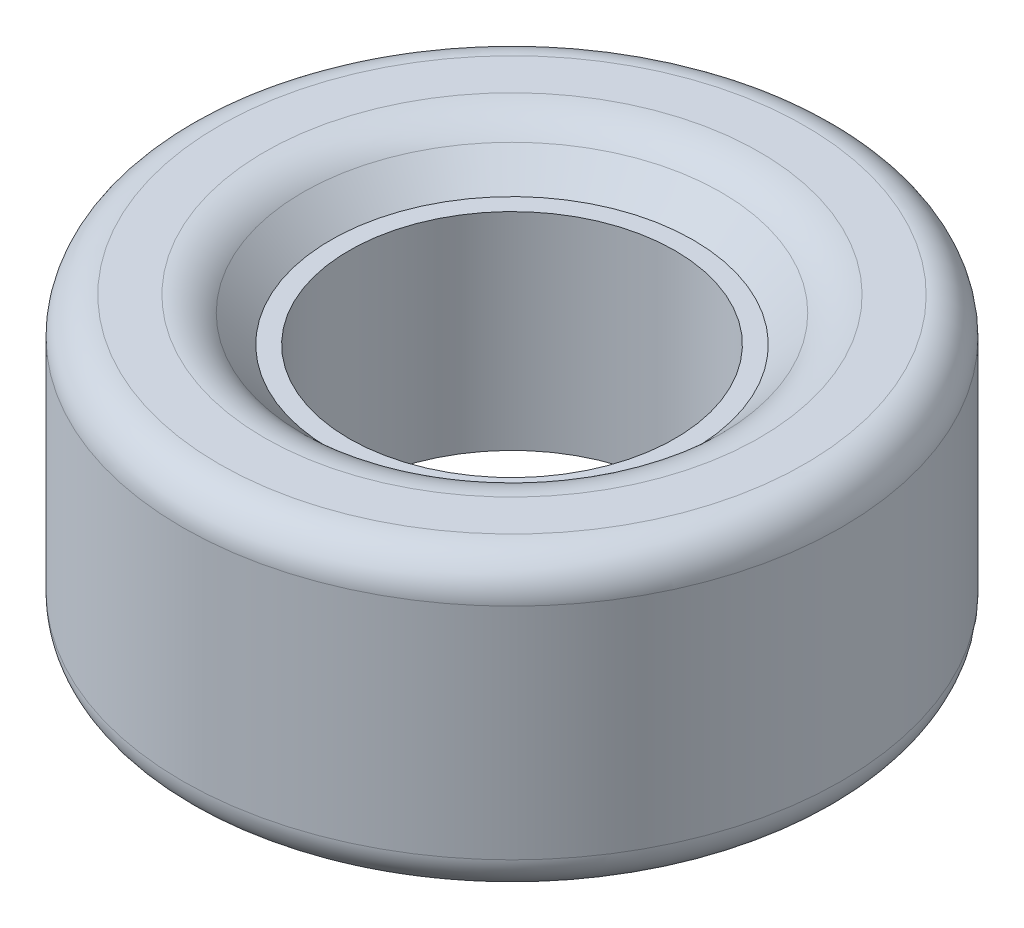
SolidWorks part; units mm, degrees
material "Rubber"
ref_plane "Front Plane" through (0, 0, 0) normal (0, 0, 1) x (1, 0, 0)
ref_plane "Top Plane" through (0, 0, 0) normal (0, 1, 0) x (1, 0, 0)
ref_plane "Right Plane" through (0, 0, 0) normal (1, 0, 0) x (0, 0, -1)
sketch "Sketch1" plane through (0, 0, 0) normal (0, 1, 0) x (1, 0, 0)
  circle A0 centre (0, 0) radius 44.5
  circle A1 centre (0, 0) radius 90
  dimension "D1" = 89
  dimension "D2" = 180
extrude "Boss-Extrude1" add sketch "Sketch1" along normal blind 80
ref_plane "Plane1" through (0, 40, 0) normal (0, -1, 0) x (-1, 0, 0)
sketch "Sketch2" plane through (0, 0, 0) normal (0, 0, 1) x (1, 0, 0)
  line L0 (0, 0) -> (0, 80) construction
  line L1 (-44.5, 0) -> (44.5, 0) construction
  line L2 (44.5, 80) -> (-44.5, 80) construction
  line L3 (61.5, 0) -> (49.5, 11.75)
  line L4 (-90, 0) -> (90, 0) construction
  line L5 (49.5, 11.75) -> (-49.5, 11.75) construction
  line L6 (49.5, 11.75) -> (44.5, 11.75)
  line L7 (44.5, 11.75) -> (-44.5, 11.75) construction
  line L8 (44.5, 11.75) -> (44.5, 0)
  line L9 (44.5, 0) -> (61.5, 0)
  dimension "D1" = 12
revolve "Cut-Revolve1" cut sketch "Sketch2" angle 360 about L0
mirror "Mirror1" about plane through (0, 40, 0) normal (0, -1, 0) of "Cut-Revolve1"
fillet "Fillet1" radius 15 2 edges at (0, 0, -61.5) (0, 80, -61.5)
fillet "Fillet2" radius 10 2 edges at (0, 0, 90) (0, 80, 90)
